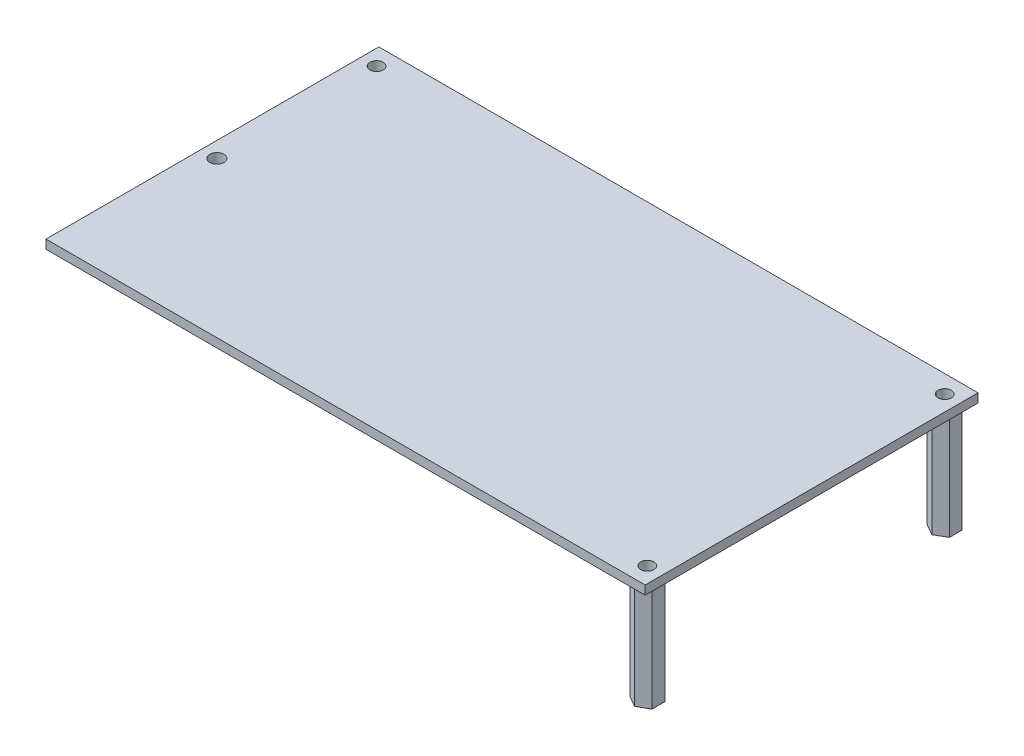
SolidWorks part; units mm, degrees
ref_plane "Спереди" through (0, 0, 0) normal (0, 0, 1) x (1, 0, 0)
ref_plane "Сверху" through (0, 0, 0) normal (0, 1, 0) x (1, 0, 0)
ref_plane "Справа" through (0, 0, 0) normal (1, 0, 0) x (0, 0, -1)
sketch "Эскиз1" plane through (0, 0, 0) normal (0, 1, 0) x (1, 0, 0)
  line L0 (0, 0) -> (135, 0)
  line L1 (0, 0) -> (0, 75)
  line L2 (135, 0) -> (135, 75)
  line L3 (0, 75) -> (135, 75)
  line L4 (3.5, 71) -> (131.5, 71) construction
  line L5 (3.5, 71) -> (3.5, 4) construction
  line L6 (131.5, 71) -> (131.5, 4) construction
  line L7 (3.5, 4) -> (131.5, 4) construction
  line L8 (67.5, 71) -> (67.5, 4) construction
  line L9 (131.5, 37.5) -> (3.5, 37.5) construction
  line L10 (67.5, 75) -> (67.5, 0) construction
  line L11 (135, 37.5) -> (0, 37.5) construction
  circle A0 centre (3.5, 71) radius 1.5
  circle A1 centre (3.5, 35) radius 1.6
  circle A2 centre (131.5, 71) radius 1.5
  circle A3 centre (131.5, 4) radius 1.5
  dimension "D5" = 3
  dimension "D6" = 3.2
  dimension "D7" = 3
  dimension "D8" = 3
  dimension "D9" = 36
  dimension "D1" = 75
  dimension "D2" = 135
  dimension "D3" = 67
  dimension "D4" = 128
extrude "Бобышка-Вытянуть1" add sketch "Эскиз1" along normal blind 2
sketch "Эскиз2" plane through (0, 0, 0) normal (0, -1, 0) x (1, 0, 0)
  line L0 (3.5, -32.1132) -> (3.5, -37.8868) construction
  line L1 (3.5, -37.8868) -> (6, -36.4434)
  line L2 (6, -36.4434) -> (6, -33.5566)
  line L3 (6, -33.5566) -> (3.5, -32.1132)
  line L4 (3.5, -32.1132) -> (1, -33.5566)
  line L5 (1, -33.5566) -> (1, -36.4434)
  line L6 (1, -36.4434) -> (3.5, -37.8868)
  line L7 (3.5, -73.8868) -> (6, -72.4434)
  line L8 (6, -72.4434) -> (6, -69.5566)
  line L9 (6, -69.5566) -> (3.5, -68.1132)
  line L10 (3.5, -68.1132) -> (1, -69.5566)
  line L11 (1, -69.5566) -> (1, -72.4434)
  line L12 (1, -72.4434) -> (3.5, -73.8868)
  line L13 (131.5, -6.8868) -> (134, -5.4434)
  line L14 (134, -5.4434) -> (134, -2.5566)
  line L15 (134, -2.5566) -> (131.5, -1.1132)
  line L16 (131.5, -1.1132) -> (129, -2.5566)
  line L17 (129, -2.5566) -> (129, -5.4434)
  line L18 (129, -5.4434) -> (131.5, -6.8868)
  line L19 (129, -72.4434) -> (131.5, -73.8868)
  line L20 (131.5, -73.8868) -> (134, -72.4434)
  line L21 (134, -72.4434) -> (134, -69.5566)
  line L22 (134, -69.5566) -> (131.5, -68.1132)
  line L23 (131.5, -68.1132) -> (129, -69.5566)
  line L24 (129, -69.5566) -> (129, -72.4434)
  line L25 (3.5, -68.1132) -> (3.5, -73.8868) construction
  line L26 (131.5, -1.1132) -> (131.5, -6.8868) construction
  line L27 (131.5, -68.1132) -> (131.5, -73.8868) construction
  circle A0 centre (3.5, -35) radius 2.5 construction
  circle A1 centre (3.5, -71) radius 2.5 construction
  circle A2 centre (131.5, -4) radius 2.5 construction
  circle A3 centre (131.5, -71) radius 2.5 construction
  circle A4 centre (3.5, -35) radius 1.6 construction
  circle A5 centre (3.5, -35) radius 1.6 construction
  dimension "D1" = 5
  dimension "D2" = 5
  dimension "D3" = 5
  dimension "D4" = 5
extrude "Бобышка-Вытянуть2" add sketch "Эскиз2" along normal blind 24
sketch "Эскиз3" plane through (0, 0, 0) normal (0, 1, 0) x (1, 0, 0)
  circle A0 centre (3.5, 71) radius 1.5 construction
  circle A2 centre (131.5, 4) radius 1.5 construction
  circle A3 centre (131.5, 71) radius 1.5 construction
  circle A4 centre (3.5, 71) radius 1.5
  circle A5 centre (3.5, 35) radius 1.6 construction
  circle A6 centre (131.5, 4) radius 1.5
  circle A7 centre (131.5, 71) radius 1.5
  circle A8 centre (3.5, 35) radius 1.6
extrude "Вырез-Вытянуть1" cut sketch "Эскиз3" against normal through all
sketch "Эскиз4" plane through (0, 2, 0) normal (0, 1, 0) x (1, 0, 0)
  line L0 (3.5, 71) -> (3.5, 35) construction
  dimension "D1" = 36
